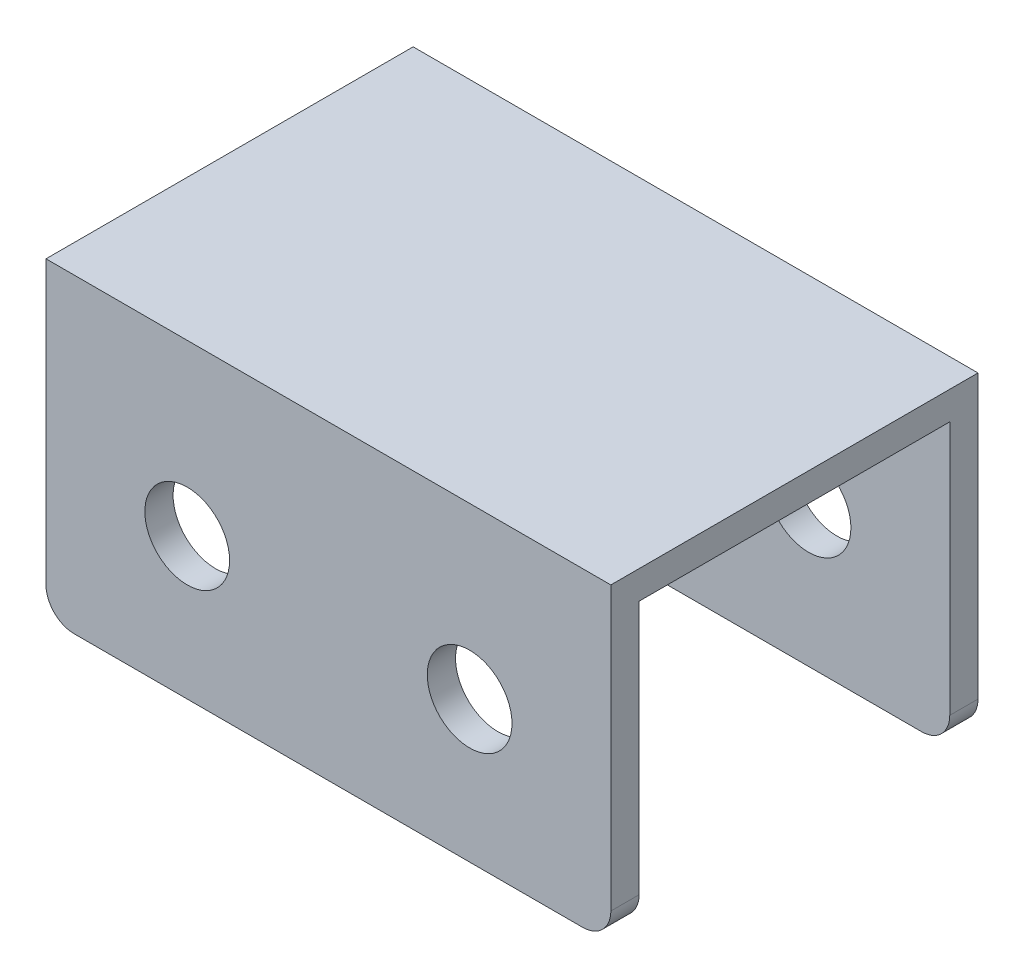
SolidWorks part; units mm, degrees
ref_plane "Front Plane" through (0, 0, 0) normal (0, 0, 1) x (1, 0, 0)
ref_plane "Top Plane" through (0, 0, 0) normal (0, 1, 0) x (1, 0, 0)
ref_plane "Right Plane" through (0, 0, 0) normal (1, 0, 0) x (0, 0, -1)
sketch "Sketch1" plane through (0, 0, 0) normal (1, 0, 0) x (0, 0, -1)
  line L0 (-27.5, -50) -> (-27.5, 0)
  line L1 (-27.5, 0) -> (27.5, 0)
  line L2 (27.5, 0) -> (27.5, -50)
  dimension "D1" = 55
  dimension "D2" = 50
extrude "Extrude-Thin1" add sketch "Sketch1" along normal mid plane 100 thin thin type one direction reverse wall 5
sketch "Sketch2" plane through (0, 0, 0) normal (0, 0, 1) x (1, 0, 0)
  line L0 (0, 0) -> (0, -50) construction
  line L1 (50, -50) -> (-50, -50) construction
  line L2 (50, -25) -> (0, -25) construction
  line L3 (50, -50) -> (50, 0) construction
  circle A0 centre (-25, -25) radius 7.5
  circle A1 centre (25, -25) radius 7.5
  dimension "D1" = 15
extrude "Cut-Extrude1" cut sketch "Sketch2" against normal through all both and the other way through all
fillet "Fillet1" radius 5 4 edges at (50, -50, -30) (-50, -50, -30) (-50, -50, 30) (50, -50, 30)
